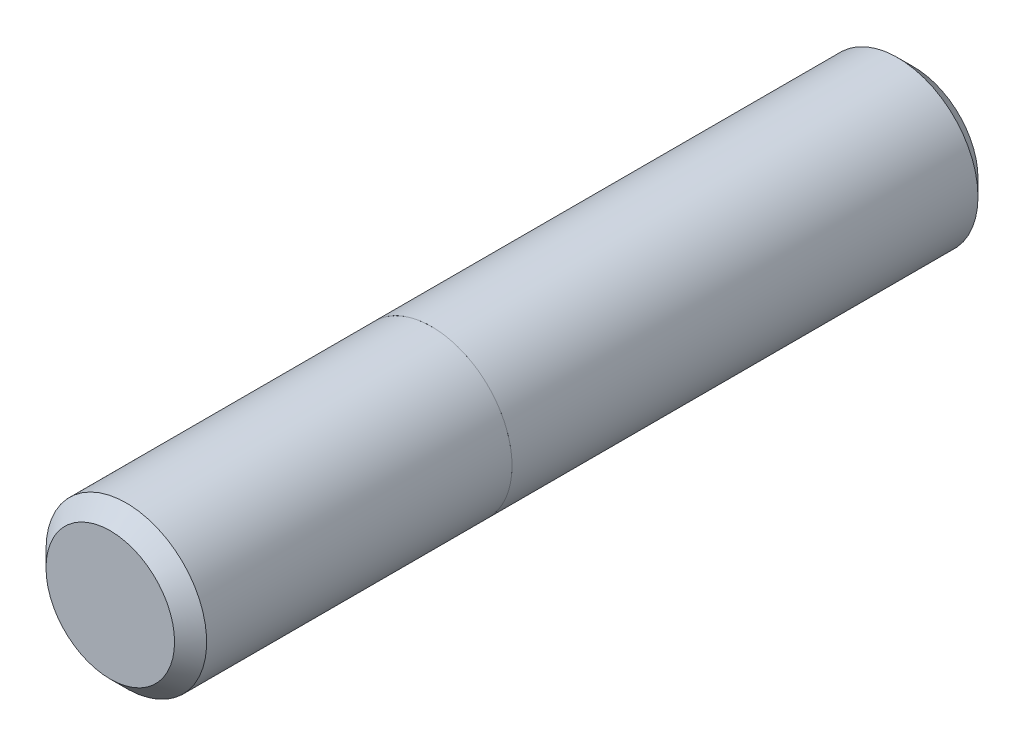
SolidWorks part; units mm, degrees
ref_plane "Ebene vorne" through (0, 0, 0) normal (0, 0, 1) x (1, 0, 0)
ref_plane "Ebene oben" through (0, 0, 0) normal (0, 1, 0) x (1, 0, 0)
ref_plane "Ebene rechts" through (0, 0, 0) normal (1, 0, 0) x (0, 0, -1)
sketch "Skizze1" plane through (0, 0, 0) normal (0, 0, 1) x (1, 0, 0)
  circle A0 centre (0, 0) radius 5
  dimension "D1" = 10
extrude "Aufsatz-Linear austragen1" add sketch "Skizze1" along normal blind 50
chamfer "Fase1" distance 1 angle 45 2 edges at (5, 0, 0) (5, 0, 50)
ref_plane "Ebene1" through (0, 0, 30) normal (0, 0, 1) x (1, 0, 0)
sketch "Szkic1" plane through (0, 0, 30) normal (0, 0, 1) x (1, 0, 0)
  circle A2 centre (0, 0) radius 4.999
  circle A3 centre (0, 0) radius 4.999
  dimension "D1" = 0.001
extrude "Wytnij-wyciągnięcie1" cut sketch "Szkic1" along normal through all flip side to cut
cosmetic thread "Oznaczenie gwintu1" parameters "D1"=5, "D2"=8.998
